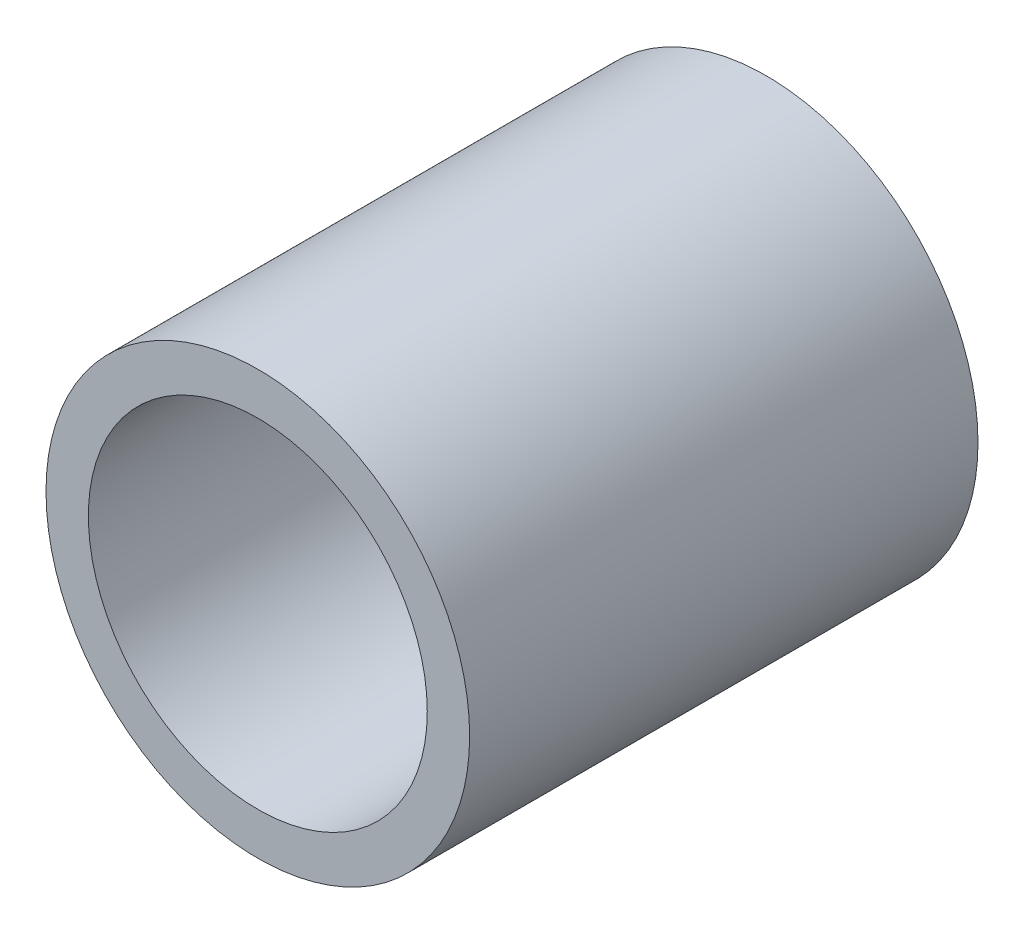
SolidWorks part; units mm, degrees
ref_plane "Front Plane" through (0, 0, 0) normal (0, 0, 1) x (1, 0, 0)
ref_plane "Top Plane" through (0, 0, 0) normal (0, 1, 0) x (1, 0, 0)
ref_plane "Right Plane" through (0, 0, 0) normal (1, 0, 0) x (0, 0, -1)
sketch "Sketch1" plane through (0, 0, 0) normal (0, 0, 1) x (1, 0, 0)
  circle A0 centre (0, 0) radius 0.125
  circle A1 centre (0, 0) radius 0.1
  dimension "D1" = 0.2
  dimension "D2" = 0.25
extrude "Boss-Extrude1" add sketch "Sketch1" along normal blind 0.3
